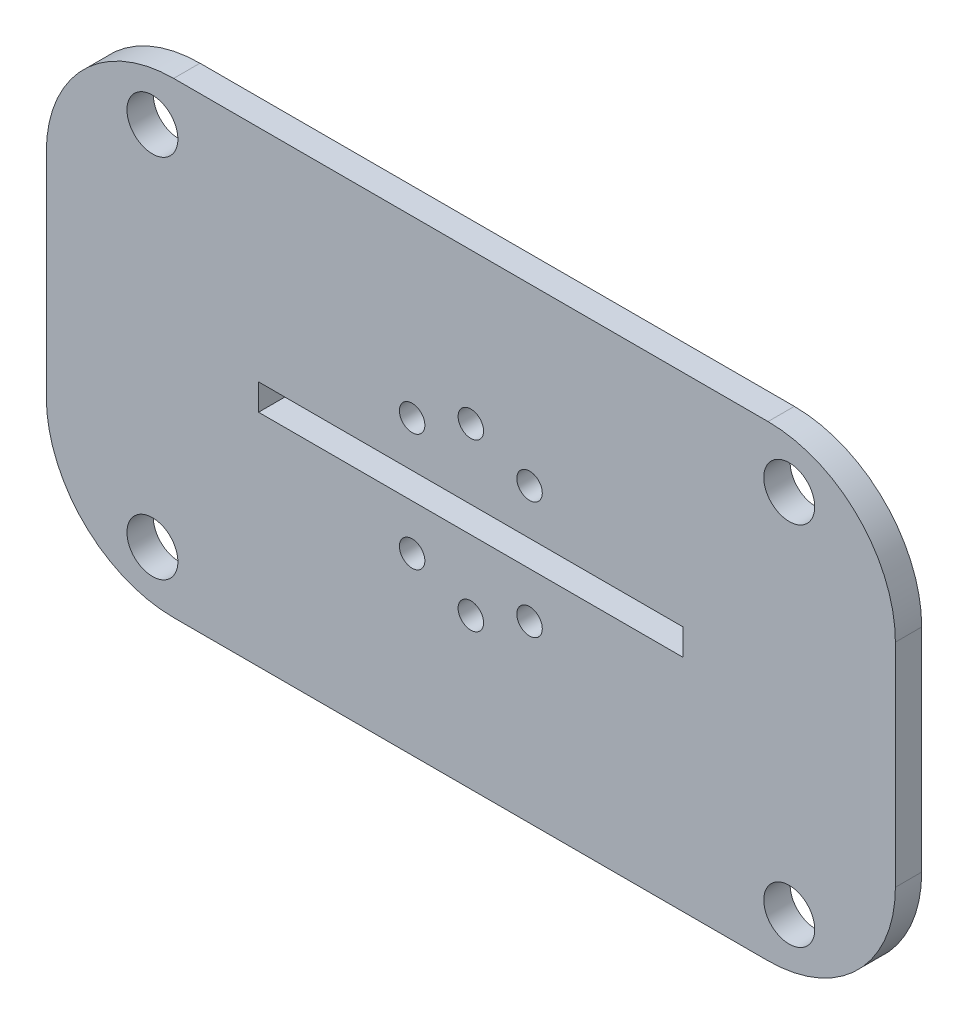
SolidWorks part; units mm, degrees
material "Teak"
ref_plane "Front Plane" through (0, 0, 0) normal (0, 0, 1) x (1, 0, 0)
ref_plane "Top Plane" through (0, 0, 0) normal (0, 1, 0) x (1, 0, 0)
ref_plane "Right Plane" through (0, 0, 0) normal (1, 0, 0) x (0, 0, -1)
sketch "Sketch1" plane through (0, 0, 0) normal (0, 0, 1) x (1, 0, 0)
  line L0 (0, 0) -> (44.0517, 0) construction
  line L1 (-50, -27.5) -> (50, -27.5)
  line L2 (-50, -27.5) -> (-50, 27.5)
  line L3 (-50, 27.5) -> (50, 27.5)
  line L4 (50, -27.5) -> (50, 27.5)
  line L5 (-50, -27.5) -> (50, 27.5) construction
  line L6 (-50, 27.5) -> (50, -27.5) construction
  line L7 (-25, -1.55) -> (25, -1.55)
  line L8 (-25, -1.55) -> (-25, 1.55)
  line L9 (-25, 1.55) -> (25, 1.55)
  line L10 (25, -1.55) -> (25, 1.55)
  line L11 (-25, -1.55) -> (25, 1.55) construction
  line L12 (-25, 1.55) -> (25, -1.55) construction
  line L13 (44.0517, 0) -> (0, 0) construction
  line L14 (0, 0) -> (0, 27.5) construction
  circle A0 centre (37.5, 21.55) radius 3
  circle A1 centre (-37.5, 21.55) radius 3
  circle A2 centre (-37.5, -21.55) radius 3
  circle A3 centre (37.5, -21.55) radius 3
  point P0 (0, 0)
  point P6 (0, 0)
  dimension "D1" = 100
  dimension "D4" = 50
  dimension "D6" = 6
  dimension "D2" = 55
  dimension "D3" = 3.1
  dimension "D5" = 20
  dimension "D7" = 75
extrude "Boss-Extrude1" add sketch "Sketch1" along normal blind 3.1
sketch "Sketch2" plane through (0, 0, 3.1) normal (0, 0, 1) x (1, 0, 0)
  line L0 (0, 0) -> (0, 25) construction
  line L1 (0, 25) -> (0, 0) construction
  line L2 (0, 0) -> (-17.6777, 17.6777) construction
  circle A0 centre (0, 0) radius 25 construction
  circle A1 centre (-6.9148, 6.9148) radius 1.5
  circle A2 centre (0, 9.779) radius 1.5
  circle A3 centre (6.9148, 6.9148) radius 1.5
  circle A4 centre (9.779, 0) radius 1.5
  circle A5 centre (6.9148, -6.9148) radius 1.5
  circle A6 centre (0, -9.779) radius 1.5
  circle A7 centre (-6.9148, -6.9148) radius 1.5
  circle A8 centre (-9.779, 0) radius 1.5
  point P23 (0, 0)
  dimension "D2" = 3
  dimension "D1" = 45
  dimension "D4" = 19.558
  dimension "D5" = 0
  dimension "D3" = 8
extrude "Cut-Extrude1" cut sketch "Sketch2" against normal through all
fillet "Fillet1" radius 15 4 edges at (-50, 27.5, 1.55) (-50, -27.5, 1.55) (50, -27.5, 1.55) (50, 27.5, 1.55)
equation "\"thick\" = 3.1mm"
equation "\"small_bearing_outer\"=12.9mm"
equation "\"servo1_L\"=40.7mm"
equation "\"servo1_W\"=20.5mm"
equation "\"servo1_H\"=43.5mm"
equation "\"servo1_hL\"=49mm"
equation "\"servo1_hW\"=10mm"
equation "\"D1@Boss-Extrude1\"=\"thick\""
equation "\"D3@Sketch1\"=\"thick\""
